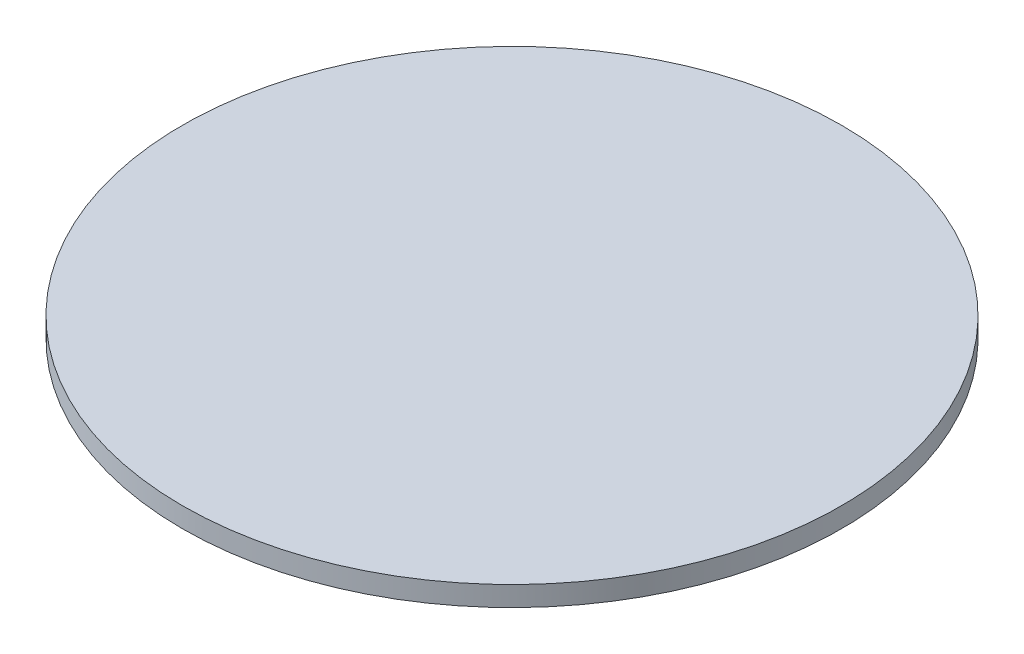
SolidWorks part; units mm, degrees
material "Glass"
ref_plane "Front Plane" through (0, 0, 0) normal (0, 0, 1) x (1, 0, 0)
ref_plane "Top Plane" through (0, 0, 0) normal (0, 1, 0) x (1, 0, 0)
ref_plane "Right Plane" through (0, 0, 0) normal (1, 0, 0) x (0, 0, -1)
sketch "Sketch1" plane through (0, 0, 0) normal (0, 1, 0) x (1, 0, 0)
  circle A0 centre (0, 0) radius 16.5
extrude "Boss-Extrude1" add sketch "Sketch1" along normal blind 1 contours A0
